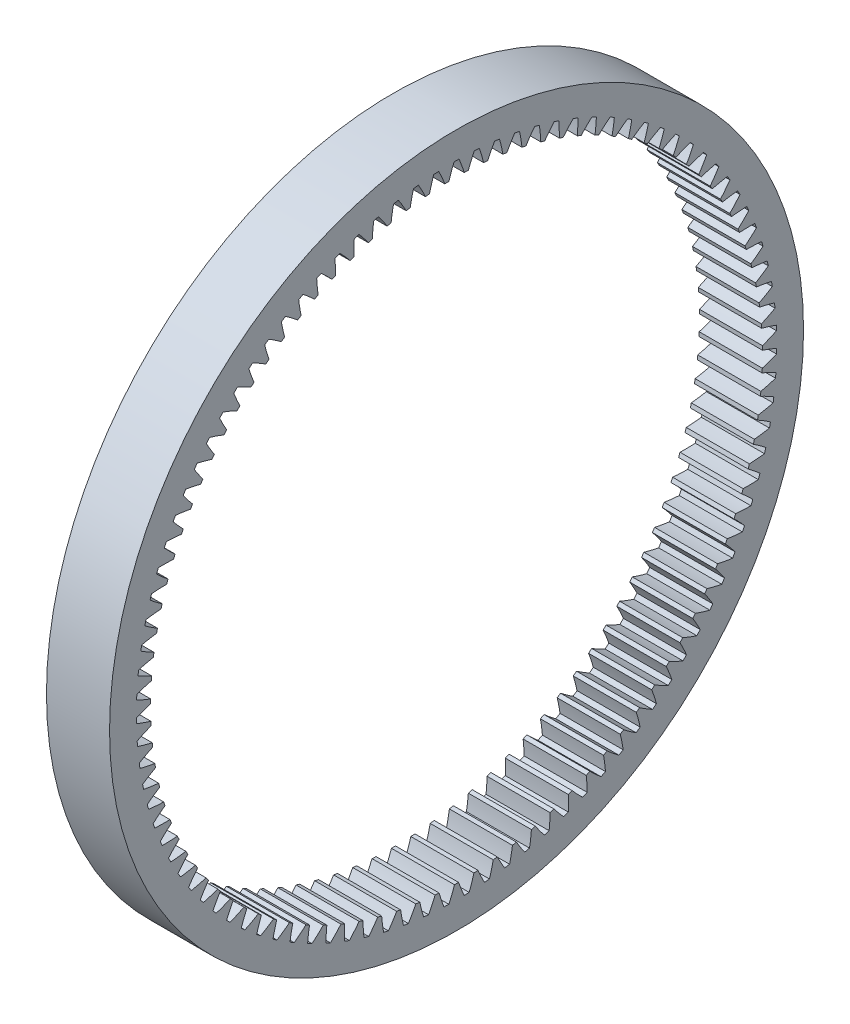
SolidWorks part; units mm, degrees
material "1.0035 (S185)"
ref_plane "Plane1" through (0, 0, 0) normal (0, 0, 1) x (1, 0, 0)
ref_plane "Plane2" through (0, 0, 0) normal (0, 1, 0) x (1, 0, 0)
ref_plane "Plane3" through (0, 0, 0) normal (1, 0, 0) x (0, 0, -1)
sketch "HoldingSke" plane through (0, 0, 0) normal (0, 1, 0) x (1, 0, 0)
  line L0 (0, 0) -> (-0.3129, -1.9754)
  line L1 (-15, 0) -> (100, 0) construction
  line L2 (0, 0) -> (-2.1039, 2.3779)
  line L3 (0, 0) -> (-11.863, 4.5341)
  line L4 (0, 0) -> (-1.351, 8.5297)
  line L5 (0, 0) -> (-23.7986, -8.8762)
  line L6 (0, 0) -> (-10.5278, -7.1032)
  line L7 (-2.1039, 2.3779) -> (3.3635, 27.1825)
  line L8 (-76.2, 2.8779) -> (-54.61, 2.8779)
  line L9 (-71.009, 38.7566) -> (-53.1078, 45.2721)
  line L10 (-76.2, 71.12) -> (104.1128, 71.12)
  line L11 (0, 0) -> (-5, 0)
  line L12 (-76.2, 101.6) -> (-76.181, 101.6)
  line L13 (24.9733, 27.94) -> (52.9518, 28.4284)
  line L14 (24.9733, 27.94) -> (24.9743, 27.94)
  line L15 (24.9733, 27.94) -> (100.4006, 29.5858)
  circle A0 centre (0, 0) radius 27.5
  circle A1 centre (0, 0) radius 12.7
  circle A2 centre (0, 0) radius 12.7
  dimension "MHD" = 25.4
  dimension "Hub_dia" = 25.4
  dimension "Diameter" = 55
  dimension "Num_teeth" = 99
  dimension "Pitch_radius" = 180.3128
  dimension "Pitch" = 2
  dimension "Width" = 5
  dimension "Overall_len" = 25.4
  dimension "Show_teeth" = 99
  dimension "Thickness" = 12.7
  dimension "OAL" = 25.4001
  dimension "T_dim" = 21.59
  dimension "Ap" = 20
  dimension "H" = 19.05
  dimension "Backlash" = 0.019
  dimension "Addendum_fac" = 1
  dimension "Dedendum_fac" = 1.25
  dimension "Clearance_fac" = 0.25
  dimension "Dedendum_add" = 0.001
  dimension "Module" = 0.5
sketch "BasProSke" plane through (0, 0, 0) normal (0, 1, 0) x (1, 0, 0)
  line L0 (-10, 0) -> (60, 0) construction
  line L1 (0, 24.25) -> (0, 27.5)
  line L2 (0, 24.25) -> (5, 24.25)
  line L3 (5, 24.25) -> (5, 27.5)
  line L4 (5, 27.5) -> (0, 27.5)
  dimension "Diameter" = 55
  dimension "Thickness" = 5
  dimension "Inside_diameter" = 48.5
revolve "Base-Revolve" add sketch "BasProSke" angle 360 about L0
sketch "TooCutSke" plane through (0, 0, 0) normal (1, 0, 0) x (0, 0, -1)
  line L3 (0.4402, 24.7461) -> (0.4402, 53.6633) construction
  line L4 (0, 0) -> (0, 59.563) construction
  line L5 (0, 0) -> (-2.1679, 68.2931) construction
  line L6 (-11.2147, 20.5862) -> (37.1596, 22.1218) construction
  circle A0 centre (0, 0) radius 24.75 construction
  circle A1 centre (0, 0) radius 25.376 construction
  circle A2 centre (0, 0) radius 20.9317 construction
  circle A3 centre (0, 0) radius 24.2246 construction
  arc A4 (0.6158, 24.2168) -> (0.1961, 25.3752) centre (-11.2147, 20.5862) ccw
  arc A5 (0.6158, 24.2168) -> (-0.6158, 24.2168) centre (0, 0) ccw
  arc A6 (0.1961, 25.3752) -> (-0.1961, 25.3752) centre (0, 0) ccw
  arc A7 (-0.1961, 25.3752) -> (-0.6158, 24.2168) centre (11.2147, 20.5862) ccw
  dimension "Pitch_dia" = 49.5
  dimension "Base_dia" = 41.8633
  dimension "Root_dia" = 50.752
  dimension "Overcut_dia" = 48.4492
  dimension "Flank_rad" = 12.375
  dimension "Half_ang" = 1.818
  dimension "Half_CT" = 0.4402
extrude "ToothCut" cut sketch "TooCutSke" along normal through all
fillet "Breaks" [suppressed] radius 0.05
fillet "RootFillets" [suppressed] radius 0.126
pattern_circular "TeethCuts" count 99 every 3.636 about axis through (-10, 0, 0) along (1, 0, 0) of "RootFillets", "Breaks", "ToothCut"
equation "' \"Module@HoldingSke\" = 6.35"
equation "' \"Num_teeth@HoldingSke\" = 24"
equation "' \"Ap@HoldingSke\" =  14.5"
equation "' \"Width@HoldingSke\" = 12"
equation "' \"Diameter@HoldingSke\" = 8 * 25.4"
equation "' \"Show_teeth@HoldingSke\" = 100"
equation "' \"Backlash@HoldingSke\" = 0.009 * 25.4"
equation "' \"Addendum_fac@HoldingSke\" = 1.0"
equation "' \"Dedendum_fac@HoldingSke\" = 1.25"
equation "' \"Dedendum_add@HoldingSke\" = 0.00005 * 25.4"
equation "' \"Clearance_fac@HoldingSke\" = 0.25"
equation "\"Pitch@HoldingSke\" = 1 / \"Module@HoldingSke\" "
equation "\"Overcut_dia@TooCutSke\" = (\"Num_teeth@HoldingSke\" - 2 * \"Addendum_fac@HoldingSke\") / \"Pitch@HoldingSke\" - 0.002 * 25.4"
equation "\"Pitch_dia@TooCutSke\" = \"Num_teeth@HoldingSke\" / \"Pitch@HoldingSke\""
equation "\"Base_dia@TooCutSke\" = \"Num_teeth@HoldingSke\" / \"Pitch@HoldingSke\" * cos((\"Ap@HoldingSke\"  * 3.14159265 / 180)) * 0.90"
equation "\"Root_dia@TooCutSke\" = \"Num_teeth@HoldingSke\"  / \"Pitch@HoldingSke\" + 2 *  \"Dedendum_fac@HoldingSke\"/ \"Pitch@HoldingSke\" + \"Dedendum_add@HoldingSke\" * 2"
equation "\"Half_ang@TooCutSke\" = 180 / \"Num_teeth@HoldingSke\""
equation "\"Half_CT@TooCutSke\" = \"Num_teeth@HoldingSke\" / \"Pitch@HoldingSke\" * sin((3.14159265 / 2 / \"Num_teeth@HoldingSke\")) / 2 + 10 * \"Backlash@HoldingSke\" / 4"
equation "\"Flank_rad@TooCutSke\" = \"Num_teeth@HoldingSke\" / \"Pitch@HoldingSke\" / 4"
equation "\"Radius@RootFillets\"= \"Clearance_fac@HoldingSke\" / \"Pitch@HoldingSke\" + \"Dedendum_add@HoldingSke\""
equation "\"Break_rad@Breaks\" = 0.02 / \"Pitch@HoldingSke\" * 5"
equation "\"Num_teeth@TeethCuts\" = int( \"Show_teeth@HoldingSke\" ) + 1"
equation "\"Num_teeth@TeethCuts\" = ((sgn( \"Num_teeth@TeethCuts\" - \"Num_teeth@HoldingSke\" )-1)*( \"Num_teeth@TeethCuts\" - \"Num_teeth@HoldingSke\" ))/-2+ \"Num_teeth@HoldingSke\""
equation "\"Num_teeth@TeethCuts\" = ((sgn( \"Num_teeth@TeethCuts\" - 2.0)+1)*( \"Num_teeth@TeethCuts\" - 2.0))/2 +2.0"
equation "\"Angle@TeethCuts\" = 360.0 / \"Num_teeth@HoldingSke\""
equation "\"Diameter@BasProSke\" = \"Num_teeth@HoldingSke\"  / \"Pitch@HoldingSke\" + 2 *  \"Dedendum_fac@HoldingSke\"/ \"Pitch@HoldingSke\" + \"Dedendum_add@HoldingSke\" * 2 + 0.002 * 25.4"
equation "\"Diameter@BasProSke\" = ((sgn( \"Diameter@BasProSke\"  - \"Diameter@HoldingSke\" )+1)*( \"Diameter@BasProSke\"  - \"Diameter@HoldingSke\" ))/2 + \"Diameter@HoldingSke\""
equation "\"Inside_diameter@BasProSke\" =  (\"Num_teeth@HoldingSke\" - 2 * \"Addendum_fac@HoldingSke\") / \"Pitch@HoldingSke\" "
equation "\"Thickness@BasProSke\"  = \"Width@HoldingSke\""
